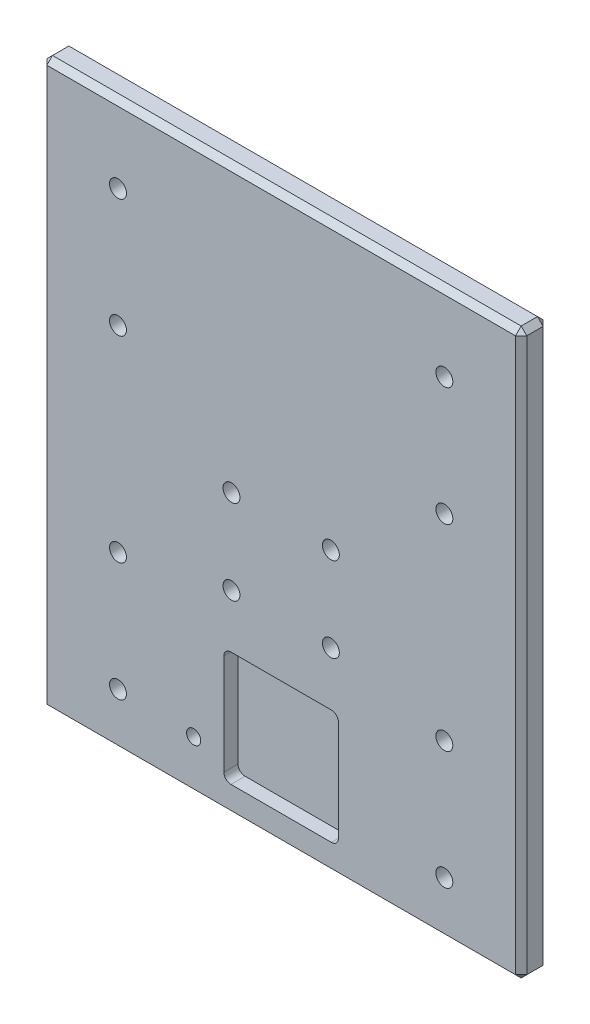
SolidWorks part; units mm, degrees
ref_plane "Front Plane" through (0, 0, 0) normal (0, 0, 1) x (1, 0, 0)
ref_plane "Top Plane" through (0, 0, 0) normal (0, 1, 0) x (1, 0, 0)
ref_plane "Right Plane" through (0, 0, 0) normal (1, 0, 0) x (0, 0, -1)
sketch "Sketch1" plane through (0, 0, 0) normal (0, 0, 1) x (1, 0, 0)
  line L1 (-53.975, -63.5) -> (53.975, -63.5)
  line L2 (-53.975, -63.5) -> (-53.975, 63.5)
  line L3 (-53.975, 63.5) -> (53.975, 63.5)
  line L4 (53.975, -63.5) -> (53.975, 63.5)
  line L5 (-53.975, -63.5) -> (53.975, 63.5) construction
  line L6 (-53.975, 63.5) -> (53.975, -63.5) construction
  point P0 (0, 0)
  dimension "D1" = 107.95
  dimension "D2" = 127
extrude "Boss-Extrude1" add sketch "Sketch1" along normal blind 6.223
chamfer "Chamfer1" distance 1.27 angle 45 12 edges at (-53.975, 0, 6.223) (-53.975, 0, 0) (-53.975, -63.5, 3.1115) (0, -63.5, 6.223) (0, -63.5, 0) (53.975, -63.5, 3.1115) (53.975, 0, 6.223) (53.975, 0, 0) (53.975, 63.5, 3.1115) (0, 63.5, 6.223) (-53.975, 63.5, 3.1115) (0, 63.5, 0)
sketch "Sketch2" plane through (0, 0, 6.223) normal (0, 0, 1) x (1, 0, 0)
  line L0 (0, 46.228) -> (0, 0) construction
  line L1 (0, 0) -> (0, -51.308) construction
  line L2 (0, 0) -> (36.703, 0) construction
  line L3 (0, 0) -> (-36.703, 0) construction
  line L4 (-53.975, 63.5) -> (-53.975, -63.5) construction
  line L5 (53.975, -63.5) -> (53.975, 63.5) construction
  line L6 (53.975, 63.5) -> (-53.975, 63.5) construction
  line L7 (-53.975, -63.5) -> (53.975, -63.5) construction
  line L8 (0, 46.228) -> (-36.703, 46.228) construction
  line L9 (-36.703, 46.228) -> (-36.703, 0) construction
  line L10 (-36.703, 0) -> (-36.703, -51.308) construction
  line L11 (-36.703, -51.308) -> (0, -51.308) construction
  line L12 (0, -51.308) -> (36.703, -51.308) construction
  line L13 (36.703, -51.308) -> (36.703, 0) construction
  line L14 (36.703, 0) -> (36.703, 46.228) construction
  line L15 (36.703, 46.228) -> (0, 46.228) construction
  circle A0 centre (-36.703, 46.228) radius 1.905
  circle A1 centre (-36.703, -51.308) radius 1.905
  circle A2 centre (36.703, -51.308) radius 1.905
  circle A3 centre (36.703, 46.228) radius 1.905
  circle A4 centre (-36.703, 19.558) radius 1.905
  circle A5 centre (-36.703, -24.638) radius 1.905
  circle A6 centre (36.703, 19.558) radius 1.905
  circle A7 centre (36.703, -24.638) radius 1.905
  point P3 (-53.975, 0)
  dimension "D9" = 3.81
  dimension "D1" = 17.272
  dimension "D2" = 17.272
  dimension "D3" = 17.272
  dimension "D4" = 12.192
  dimension "D5" = 26.67
  dimension "D6" = 26.67
  dimension "D7" = 26.67
  dimension "D8" = 26.67
extrude "Cut-Extrude1" cut sketch "Sketch2" against normal through all
cosmetic thread "Cosmetic Thread1" parameters "D2"=4.826
cosmetic thread "Cosmetic Thread2" parameters "D2"=4.826
cosmetic thread "Cosmetic Thread3" parameters "D2"=4.826
cosmetic thread "Cosmetic Thread4" parameters "D2"=4.826
cosmetic thread "Cosmetic Thread5" parameters "D2"=4.826
cosmetic thread "Cosmetic Thread6" parameters "D2"=4.826
cosmetic thread "Cosmetic Thread7" parameters "D2"=4.826
cosmetic thread "Cosmetic Thread8" parameters "D2"=4.826
sketch "Sketch3" plane through (0, 0, 6.223) normal (0, 0, 1) x (1, 0, 0)
  line L0 (0, -104.9548) -> (0, 82.5356) construction
  line L1 (52.705, -63.5) -> (-52.705, -63.5) construction
  line L2 (-11.176, -19.304) -> (11.176, -19.304) construction
  line L3 (-11.176, -19.304) -> (-11.176, -0.254) construction
  line L4 (-11.176, -0.254) -> (11.176, -0.254) construction
  line L5 (11.176, -19.304) -> (11.176, -0.254) construction
  line L6 (-11.176, -19.304) -> (11.176, -0.254) construction
  line L7 (-11.176, -0.254) -> (11.176, -19.304) construction
  circle A0 centre (-11.176, -0.254) radius 1.905
  circle A1 centre (11.176, -0.254) radius 1.905
  circle A2 centre (11.176, -19.304) radius 1.905
  circle A3 centre (-11.176, -19.304) radius 1.905
  point P1 (0, -9.779)
  dimension "D4" = 3.81
  dimension "D1" = 22.352
  dimension "D2" = 19.05
  dimension "D3" = 44.196
extrude "Cut-Extrude2" cut sketch "Sketch3" against normal through all
cosmetic thread "Cosmetic Thread9" parameters "D2"=4.826
cosmetic thread "Cosmetic Thread10" parameters "D2"=4.826
cosmetic thread "Cosmetic Thread11" parameters "D2"=4.826
cosmetic thread "Cosmetic Thread12" parameters "D2"=4.826
sketch "Sketch4" plane through (0, 0, 6.223) normal (0, 0, 1) x (1, 0, 0)
  line L0 (0, 87.4323) -> (0, -99.0569) construction
  line L1 (52.705, -63.5) -> (-52.705, -63.5) construction
  line L2 (-12.8905, -57.15) -> (12.8905, -57.15)
  line L3 (-12.8905, -57.15) -> (-12.8905, -31.369)
  line L4 (-12.8905, -31.369) -> (12.8905, -31.369)
  line L5 (12.8905, -57.15) -> (12.8905, -31.369)
  line L6 (-12.8905, -57.15) -> (12.8905, -31.369) construction
  line L7 (-12.8905, -31.369) -> (12.8905, -57.15) construction
  point P1 (0, -44.2595)
  dimension "D1" = 25.781
  dimension "D2" = 25.781
  dimension "D3" = 6.35
extrude "Cut-Extrude3" cut sketch "Sketch4" against normal blind 3.175
fillet "Fillet1" radius 1.5875 4 edges at (-12.8905, -31.369, 4.6355) (-12.8905, -57.15, 4.6355) (12.8905, -57.15, 4.6355) (12.8905, -31.369, 4.6355)
sketch "Sketch5" plane through (0, 0, 6.223) normal (0, 0, 1) x (1, 0, 0)
  line L0 (52.705, -63.5) -> (-52.705, -63.5) construction
  line L1 (-53.975, -62.23) -> (-53.975, 62.23) construction
  circle A0 centre (-19.685, -52.07) radius 1.5875
  dimension "D1" = 3.175
  dimension "D2" = 11.43
  dimension "D3" = 34.29
extrude "Cut-Extrude4" cut sketch "Sketch5" against normal through all
